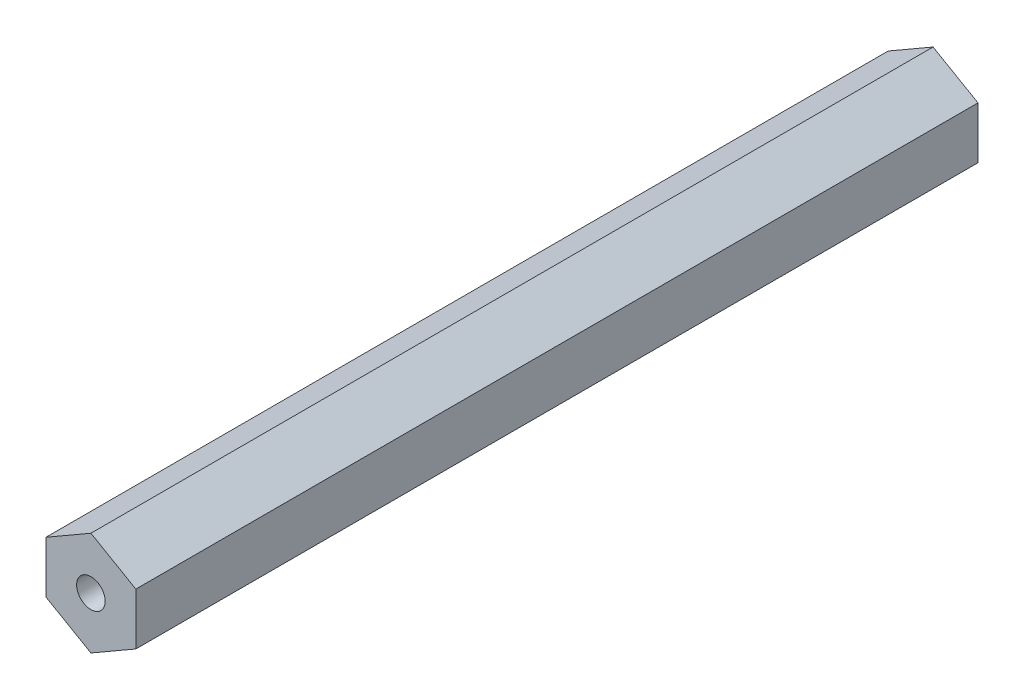
SolidWorks part; units mm, degrees
material "7075-T6 (SN)"
ref_plane "Front Plane" through (0, 0, 0) normal (0, 0, 1) x (1, 0, 0)
ref_plane "Top Plane" through (0, 0, 0) normal (0, 1, 0) x (1, 0, 0)
ref_plane "Right Plane" through (0, 0, 0) normal (1, 0, 0) x (0, 0, -1)
sketch "Sketch1" plane through (0, 0, 0) normal (0, 0, 1) x (1, 0, 0)
  line L7 (0, 7.3323) -> (-6.35, 3.6662)
  line L8 (-6.35, 3.6662) -> (-6.35, -3.6662)
  line L9 (-6.35, -3.6662) -> (0, -7.3323)
  line L10 (0, -7.3323) -> (6.35, -3.6662)
  line L11 (6.35, -3.6662) -> (6.35, 3.6662)
  line L12 (6.35, 3.6662) -> (0, 7.3323)
  circle A0 centre (0, 0) radius 6.35 construction
  dimension "D1" = 12.7
extrude "Boss-Extrude1" add sketch "Sketch1" along normal blind 119.0625 contours L7 L8 L9 L10 L11 L12
sketch "Sketch8" plane through (0, 0, 0) normal (0, 0, -1) x (-1, 0, 0)
  point P0 (0, 0)
hole_wizard "1/4-20 Tapped Hole2" positions "Sketch11" profile "Sketch12" tap size "1/4-20" standard "ANSI Inch"
sketch "Sketch11" plane through (0, 0, 0) normal (0, 0, -1) x (-1, 0, 0)
  point P0 (0, 0)
cosmetic thread "Hole Thread5" parameters "D1"=12.7, "D2"=6.35
sketch "Sketch12" plane through (0, 0, 0) normal (1, 0, 0) x (0, 1, 0)
  line L0 (0, 0) -> (0, 18.0438)
  line L1 (0, 18.0438) -> (2.5527, 16.51)
  line L2 (2.5527, 16.51) -> (2.5527, 0)
  line L5 (2.5527, 0) -> (0, 0)
  line L10 (0, 18.0438) -> (-2.5527, 16.51) construction
  line L11 (0, -6.35) -> (0, 107.95) construction
  dimension "Tap Drill Dia." = 5.1054
  dimension "Tap Drill Depth" = 16.51
  dimension "Drill Angle" = 118
sketch "Sketch14" plane through (0, 0, 119.0625) normal (0, 0, 1) x (1, 0, 0)
  line L7 (6.35, 3.6662) -> (0, 7.3323)
  line L8 (0, 7.3323) -> (-6.35, 3.6662)
  line L9 (6.35, 3.6662) -> (0, 7.3323)
  line L10 (-6.35, 3.6662) -> (-6.35, -3.6662)
  line L11 (-6.35, 3.6662) -> (-6.35, -3.6662)
  line L12 (-6.35, -3.6662) -> (0, -7.3323)
  line L14 (0, 7.3323) -> (-6.35, 3.6662)
  line L19 (-6.35, -3.6662) -> (0, -7.3323)
  line L20 (0, -7.3323) -> (6.35, -3.6662)
  line L21 (0, -7.3323) -> (6.35, -3.6662)
  line L22 (6.35, -3.6662) -> (6.35, 3.6662)
  line L23 (6.35, -3.6662) -> (6.35, 3.6662)
  dimension "D1" = 0
hole_wizard "#10-32 Tapped Hole1" positions "Sketch15" profile "Sketch16" tap size "#10-32" standard "ANSI Inch"
sketch "Sketch15" plane through (0, 0, 119.0625) normal (0, 0, 1) x (1, 0, 0)
  point P0 (0, 0)
sketch "Sketch16" plane through (0, 0, 119.0625) normal (1, 0, 0) x (0, -1, 0)
  line L0 (0, 0) -> (0, 14.8277)
  line L1 (0, 14.8277) -> (2.0193, 13.6144)
  line L2 (2.0193, 13.6144) -> (2.0193, 0)
  line L5 (2.0193, 0) -> (0, 0)
  line L10 (0, 14.8277) -> (-2.0193, 13.6144) construction
  line L11 (0, -6.35) -> (0, 107.95) construction
  dimension "Tap Drill Dia." = 4.0386
  dimension "Tap Drill Depth" = 13.6144
  dimension "Drill Angle" = 118
cosmetic thread "Hole Thread6" parameters "D1"=9.652, "D2"=4.826
